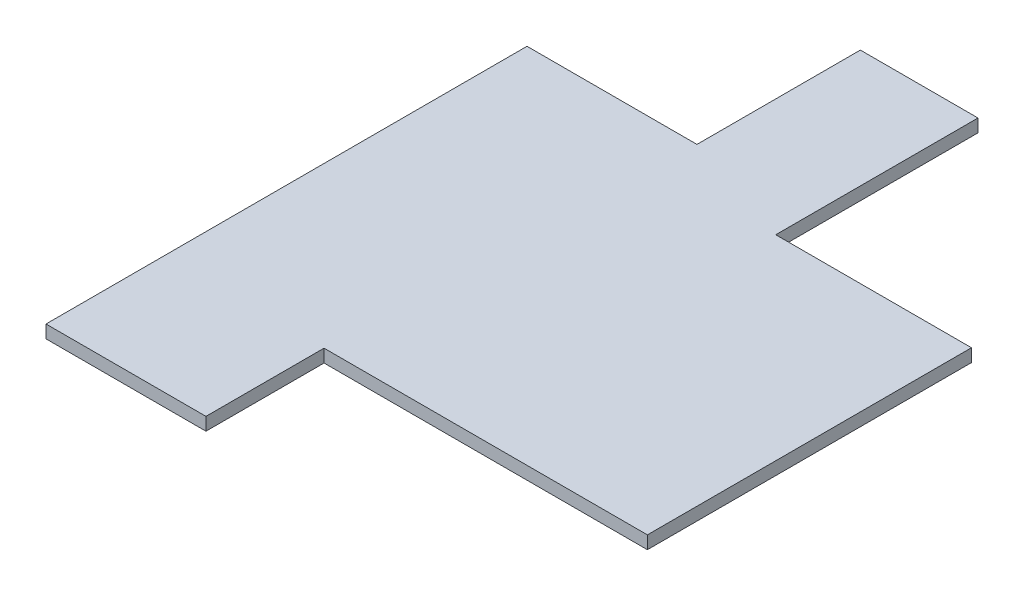
SolidWorks part; units mm, degrees
ref_plane "Plan de face" through (0, 0, 0) normal (0, 0, 1) x (1, 0, 0)
ref_plane "Plan de dessus" through (0, 0, 0) normal (0, 1, 0) x (1, 0, 0)
ref_plane "Plan de droite" through (0, 0, 0) normal (1, 0, 0) x (0, 0, -1)
sketch "Esquisse1" plane through (0, 0, 0) normal (0, 1, 0) x (1, 0, 0)
  line L0 (-0.44, 0) -> (0.44, 0) construction
  line L1 (-15, -20) -> (-5.071, -20)
  line L2 (-15, -20) -> (-15, 9.8581)
  line L3 (-4.4509, 20) -> (2.8517, 20)
  line L4 (15, -12.6697) -> (15, 7.4469)
  line L5 (-15, -20) -> (15, 20) construction
  line L6 (-7.3936, 9.8581) -> (15, -20) construction
  line L7 (-15, 9.8581) -> (-4.4509, 9.8581)
  line L8 (-4.4509, 9.8581) -> (-4.4509, 20)
  line L9 (-5.071, -20) -> (-5.071, -12.6697)
  line L10 (-5.071, -12.6697) -> (15, -12.6697)
  line L11 (15, 7.4469) -> (2.8517, 7.4469)
  line L12 (2.8517, 7.4469) -> (2.8517, 20)
  point P1 (0, 0)
  dimension "D1" = 30
  dimension "D2" = 40
extrude "Boss.-Extru.1" add sketch "Esquisse1" along normal mid plane 0.8
